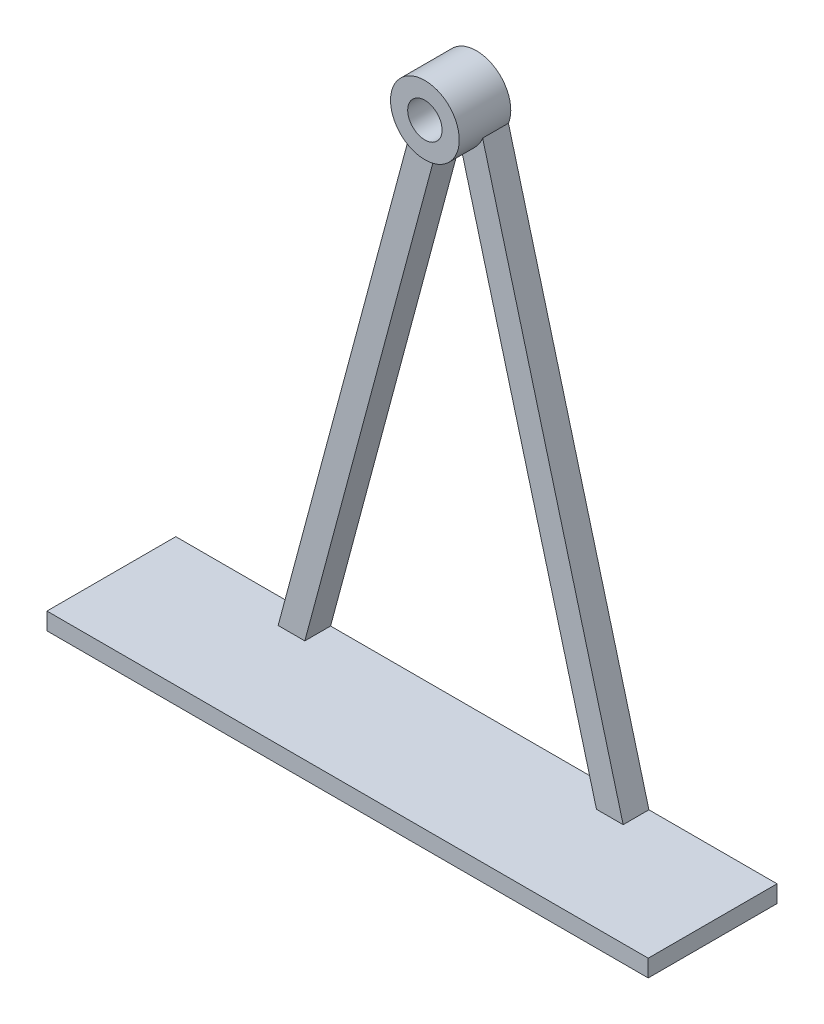
SolidWorks part; units mm, degrees
ref_plane "前视基准面" through (0, 0, 0) normal (0, 0, 1) x (1, 0, 0)
ref_plane "上视基准面" through (0, 0, 0) normal (0, 1, 0) x (1, 0, 0)
ref_plane "右视基准面" through (0, 0, 0) normal (1, 0, 0) x (0, 0, -1)
other "Configuration Table"
sketch "草图3" plane through (0, 0, 0) normal (0, 0, 1) x (1, 0, 0)
  circle A2 centre (0, 0) radius 8
  circle A3 centre (0, 0) radius 4
  dimension "D2" = 16
  dimension "D3" = 8
extrude "凸台-拉伸-转轴" add sketch "草图3" along normal blind 12
sketch "草图6" plane through (0, 0, 0) normal (0, 0, 1) x (1, 0, 0)
  line L2 (-33.9574, -125) -> (-2.5, -7.5993)
  line L4 (-40.1691, -125) -> (-33.9574, -125)
  line L5 (-40.1691, -125) -> (-7.4539, -2.9052)
  line L6 (0, 0) -> (0, -125) construction
  line L7 (0, -125) -> (-33.9574, -125) construction
  circle A0 centre (0, 0) radius 8 construction
  circle A1 centre (0, 0) radius 8
  dimension "D1" = 6
  dimension "D4" = 125
  dimension "D5" = 75
  dimension "D7" = 5
extrude "凸台-拉伸-支脚" add sketch "草图6" along normal offset from surface (6 mm away) 6 contours A1 L5 L4 L2 up to face at (8, 0, 12)
mirror "镜向-支脚" about plane through (0, 0, 0) normal (1, 0, 0) of "凸台-拉伸-支脚"
sketch "草图7" plane through (0, -125, 0) normal (0, -1, 0) x (1, 0, 0)
  line L0 (-70, 30) -> (70, 30)
  line L1 (70, 30) -> (70, 0)
  line L2 (70, 0) -> (-70, 0)
  line L3 (-70, 0) -> (-70, 30)
  line L4 (0, 0) -> (0, 30) construction
  dimension "D1" = 140
  dimension "D2" = 30
extrude "凸台-拉伸-底座" add sketch "草图7" along normal blind 4
